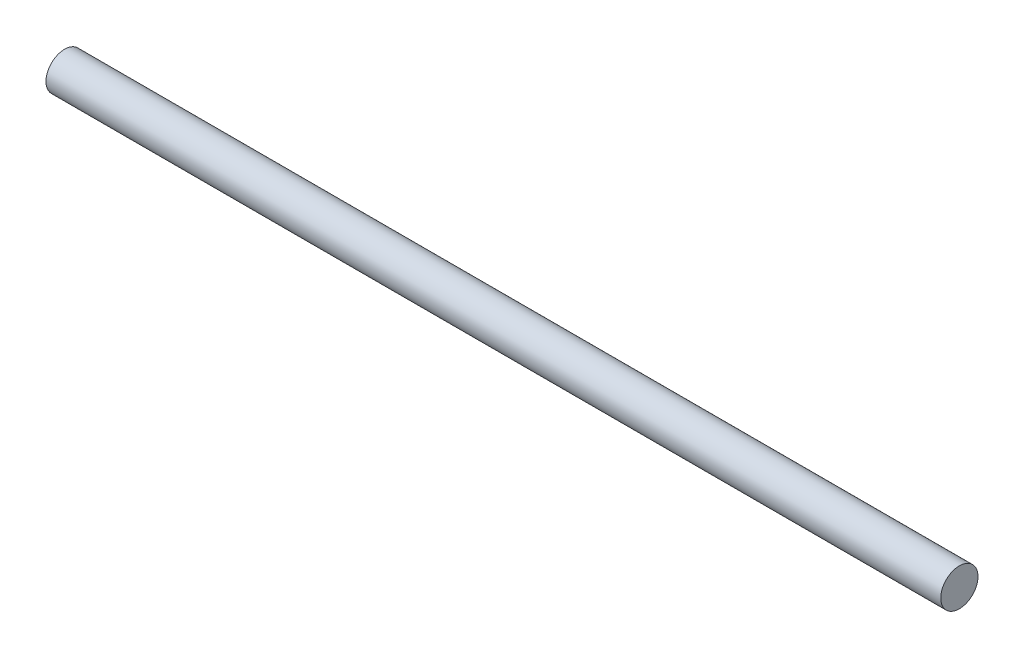
SolidWorks part; units mm, degrees
material "6061-T6 (SS)"
ref_plane "Front Plane" through (0, 0, 0) normal (0, 0, 1) x (1, 0, 0)
ref_plane "Top Plane" through (0, 0, 0) normal (0, 1, 0) x (1, 0, 0)
ref_plane "Right Plane" through (0, 0, 0) normal (1, 0, 0) x (0, 0, -1)
sketch "Sketch1" plane through (0, 0, 0) normal (1, 0, 0) x (0, 0, -1)
  circle A0 centre (0, 0) radius 4.7625
  dimension "D1" = 9.525
extrude "Boss-Extrude1" add sketch "Sketch1" along normal blind 228.6
